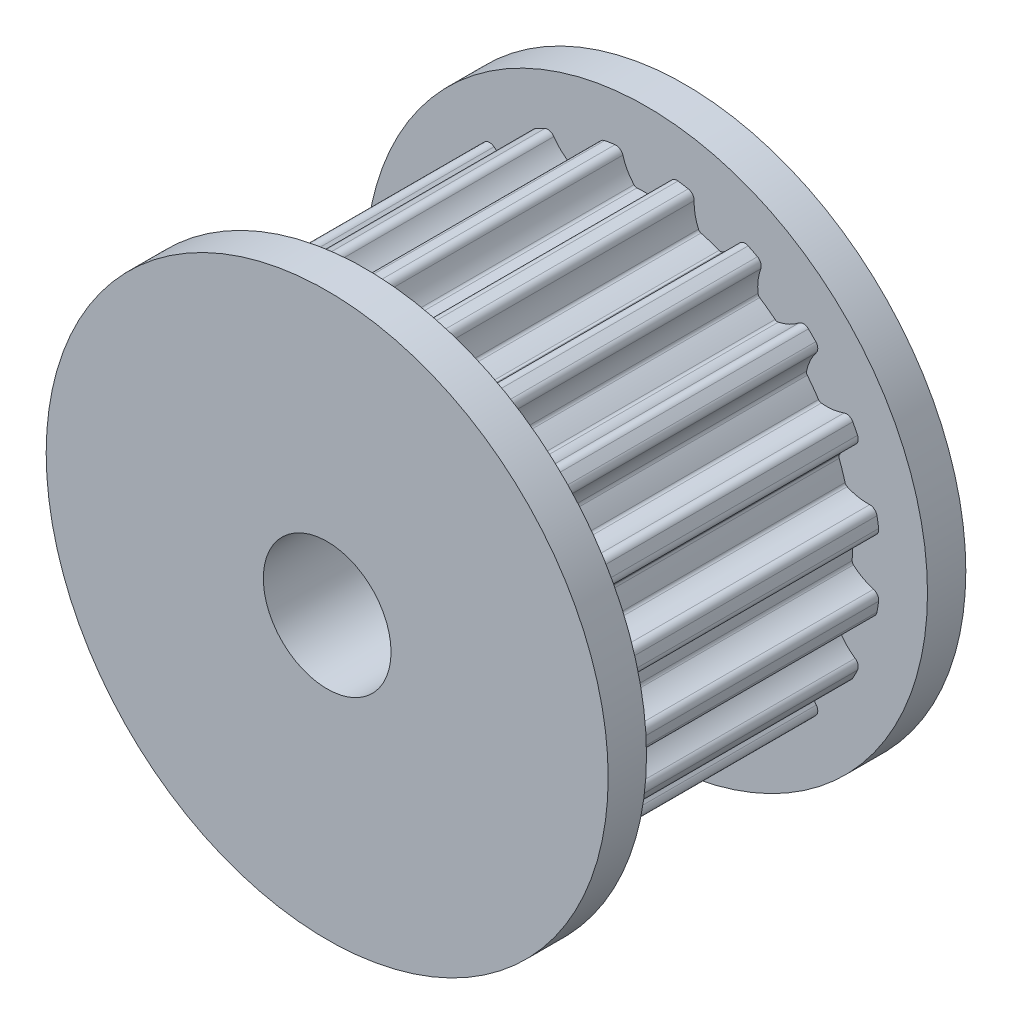
SolidWorks part; units mm, degrees
material "6061-T6 (SS)"
ref_plane "前基準面" through (0, 0, 0) normal (0, 0, 1) x (1, 0, 0)
ref_plane "上基準面" through (0, 0, 0) normal (0, 1, 0) x (1, 0, 0)
ref_plane "右基準面" through (0, 0, 0) normal (1, 0, 0) x (0, 0, -1)
sketch "草圖1" plane through (0, 0, 0) normal (0, 0, 1) x (1, 0, 0)
  circle A0 centre (0, 0) radius 9.17
  dimension "D1" = 18.34
extrude "填料-伸長1" add sketch "草圖1" along normal mid plane 11
sketch "草圖2" plane through (0, 0, 5.5) normal (0, 0, 1) x (1, 0, 0)
  line L0 (0, 0) -> (0, 9.17) construction
  line L1 (0, 9.17) -> (0, 9.424) construction
  line L2 (-0.975, 9.424) -> (0.975, 9.424) construction
  circle A0 centre (0, 0) radius 9.17 construction
  arc A1 (-0.3728, 8.0514) -> (0.3728, 8.0514) centre (0, 0) cw
  arc A2 (-0.3728, 8.0514) -> (-0.4911, 8.1007) centre (-0.3798, 8.2012) cw
  arc A3 (-0.4911, 8.1007) -> (-0.9252, 8.8857) centre (0.975, 9.424) cw
  arc A4 (-1.2322, 9.0868) -> (-0.9252, 8.8857) centre (-1.1946, 8.8094) cw
  arc A5 (0.3728, 8.0514) -> (0.4911, 8.1007) centre (0.3798, 8.2012) ccw
  arc A6 (0.4911, 8.1007) -> (0.9252, 8.8857) centre (-0.975, 9.424) ccw
  arc A7 (1.2322, 9.0868) -> (0.9252, 8.8857) centre (1.1946, 8.8094) ccw
  arc A8 (-1.2322, 9.0868) -> (1.2322, 9.0868) centre (0, 0) cw
  dimension "D1" = 0.15
  dimension "D2" = 1.975
  dimension "D3" = 0.28
  dimension "D4" = 1.11
  dimension "D5" = 0.254
  dimension "D6" = 1.95
extrude "除料-伸長1" cut sketch "草圖2" against normal through all and the other way through all
pattern_circular "環狀複製排列1" count 20 over 360 about axis through (0, 0, 0) along (0, 0, 1) of "除料-伸長1"
sketch "草圖3" plane through (0, 0, 5.5) normal (0, 0, 1) x (1, 0, 0)
  circle A0 centre (0, 0) radius 11
  dimension "D1" = 22
extrude "填料-伸長2" add sketch "草圖3" along normal blind 1.5
sketch "草圖9" plane through (0, 0, -5.5) normal (0, 0, -1) x (-1, 0, 0)
  circle A0 centre (0, 0) radius 11
  circle A1 centre (0, 0) radius 11 construction
extrude "填料-伸長3" add sketch "草圖9" along normal blind 1.5
sketch "草圖4" plane through (0, 0, 7) normal (0, 0, 1) x (1, 0, 0)
  circle A0 centre (0, 0) radius 2.5
  dimension "D1" = 5
extrude "除料-伸長2" cut sketch "草圖4" against normal through all
sketch "草圖10" plane through (0, 0, 0) normal (0, 1, 0) x (1, 0, 0)
  circle A0 centre (0, 0) radius 2
  dimension "D1" = 4
extrude "除料-伸長3" cut sketch "草圖10" against normal through all
sketch "草圖11" plane through (0, 0, 0) normal (1, 0, 0) x (0, 0, -1)
  circle A0 centre (0, 0) radius 2
  dimension "D1" = 4
extrude "除料-伸長4" cut sketch "草圖11" against normal through all
